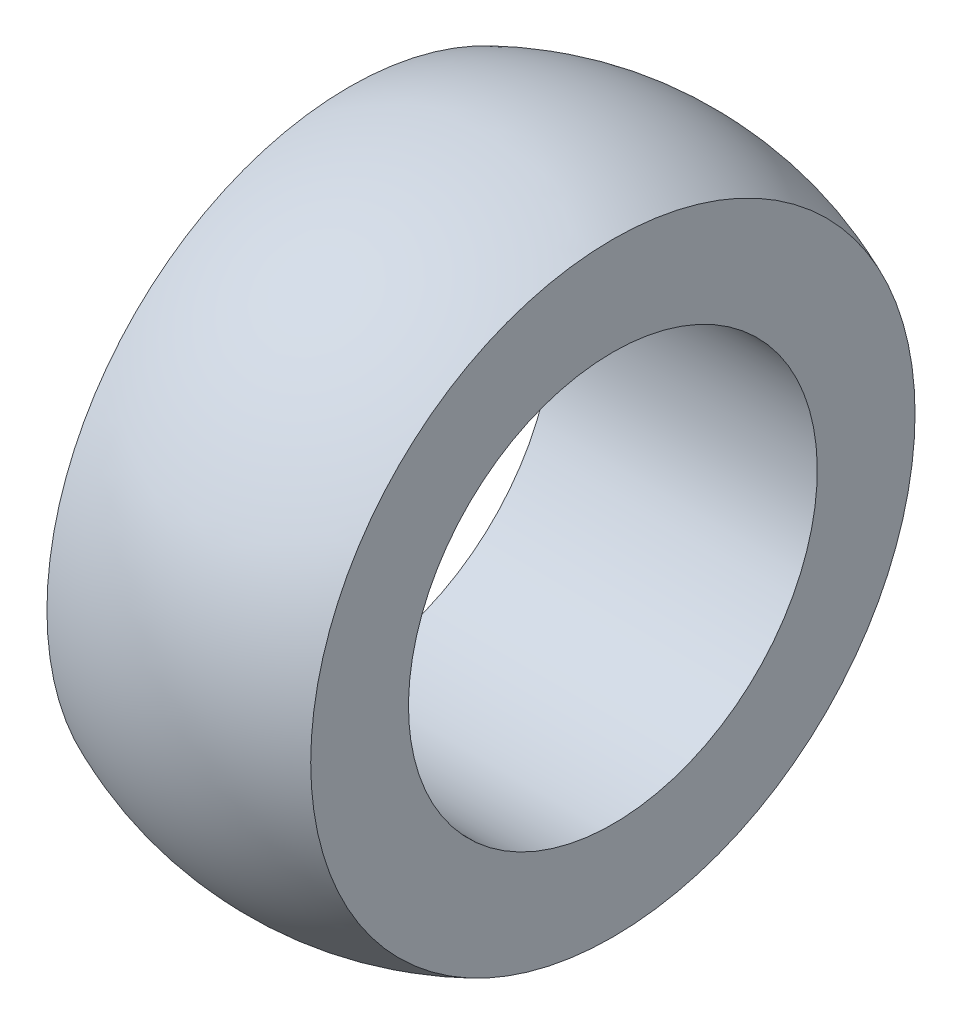
SolidWorks part; units mm, degrees
ref_plane "Front Plane" through (0, 0, 0) normal (0, 0, 1) x (1, 0, 0)
ref_plane "Top Plane" through (0, 0, 0) normal (0, 1, 0) x (1, 0, 0)
ref_plane "Right Plane" through (0, 0, 0) normal (1, 0, 0) x (0, 0, -1)
sketch "Sketch1" plane through (0, 0, 0) normal (0, 0, 1) x (1, 0, 0)
  line L0 (11.3859, 0) -> (-6.35, 0) construction
  line L4 (-2.54, 3.937) -> (-2.54, 5.8199)
  line L5 (-2.54, 3.937) -> (2.54, 3.937)
  line L6 (2.54, 3.937) -> (2.54, 5.8199)
  arc A0 (2.54, 5.8199) -> (-2.54, 5.8199) centre (0, 0) ccw
  dimension "D1" = 6.35
  dimension "D2" = 3.937
  dimension "D3" = 5.08
revolve "Revolve1" add sketch "Sketch1" angle 360 about L0
